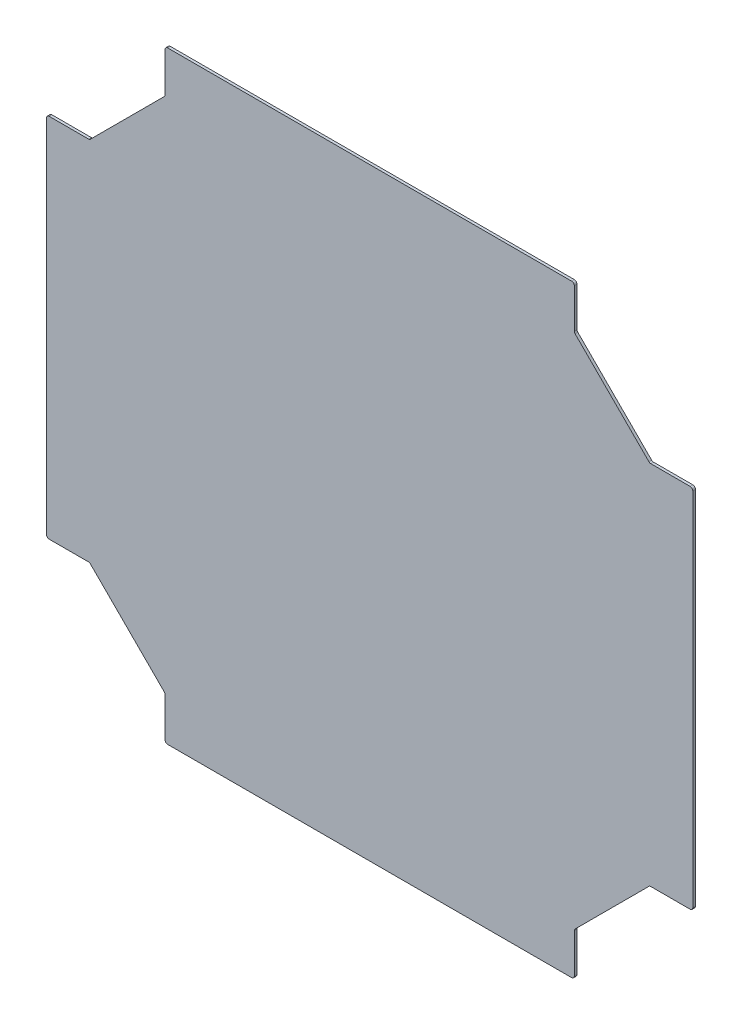
SolidWorks part; units mm, degrees
material "PC High Viscosity"
ref_plane "Front Plane" through (0, 0, 0) normal (0, 0, 1) x (1, 0, 0)
ref_plane "Top Plane" through (0, 0, 0) normal (0, 1, 0) x (1, 0, 0)
ref_plane "Right Plane" through (0, 0, 0) normal (1, 0, 0) x (0, 0, -1)
sketch "Sketch1" plane through (0, 0, 0) normal (0, 0, 1) x (1, 0, 0)
  line L1 (0, 0) -> (762, 0)
  line L2 (0, 0) -> (0, 711.2)
  line L3 (0, 711.2) -> (762, 711.2)
  line L4 (762, 0) -> (762, 711.2)
  dimension "D1" = 711.2
  dimension "D2" = 762
extrude "Boss-Extrude1" add sketch "Sketch1" along normal blind 3.175
sketch "Sketch2" plane through (0, 0, 3.175) normal (0, 0, 1) x (1, 0, 0)
  line L0 (0, 355.6) -> (762, 355.6) construction
  line L1 (0, 711.2) -> (0, 0) construction
  line L2 (762, 0) -> (762, 711.2) construction
  line L3 (381, 711.2) -> (381, 0) construction
  line L4 (762, 711.2) -> (0, 711.2) construction
  line L5 (0, 0) -> (762, 0) construction
  line L6 (0, 571.5) -> (50.8, 571.5)
  line L7 (50.8, 571.5) -> (139.7, 660.4)
  line L8 (139.7, 660.4) -> (139.7, 711.2)
  line L9 (139.7, 50.8) -> (139.7, 0)
  line L10 (50.8, 139.7) -> (139.7, 50.8)
  line L11 (0, 139.7) -> (50.8, 139.7)
  line L12 (762, 139.7) -> (711.2, 139.7)
  line L13 (711.2, 139.7) -> (622.3, 50.8)
  line L14 (622.3, 50.8) -> (622.3, 0)
  line L15 (622.3, 660.4) -> (622.3, 711.2)
  line L16 (711.2, 571.5) -> (622.3, 660.4)
  line L17 (762, 571.5) -> (711.2, 571.5)
  line L18 (0, 571.5) -> (0, 711.2)
  line L19 (0, 711.2) -> (139.7, 711.2)
  line L20 (0, 139.7) -> (0, 0)
  line L21 (0, 0) -> (139.7, 0)
  line L22 (622.3, 0) -> (762, 0)
  line L23 (762, 0) -> (762, 139.7)
  line L24 (762, 571.5) -> (762, 711.2)
  line L25 (762, 711.2) -> (622.3, 711.2)
  dimension "D1" = 50.8
  dimension "D2" = 50.8
  dimension "D3" = 139.7
  dimension "D4" = 139.7
extrude "Cut-Extrude1" cut sketch "Sketch2" against normal through all
fillet "Fillet1" radius 3.175 16 edges at (0, 139.7, 1.5875) (50.8, 139.7, 1.5875) (139.7, 50.8, 1.5875) (139.7, 0, 1.5875) (622.3, 0, 1.5875) (622.3, 50.8, 1.5875) (711.2, 139.7, 1.5875) (762, 139.7, 1.5875) (762, 571.5, 1.5875) (711.2, 571.5, 1.5875) (139.7, 660.4, 1.5875) (50.8, 571.5, 1.5875) (622.3, 660.4, 1.5875) (622.3, 711.2, 1.5875) (139.7, 711.2, 1.5875) (0, 571.5, 1.5875)
